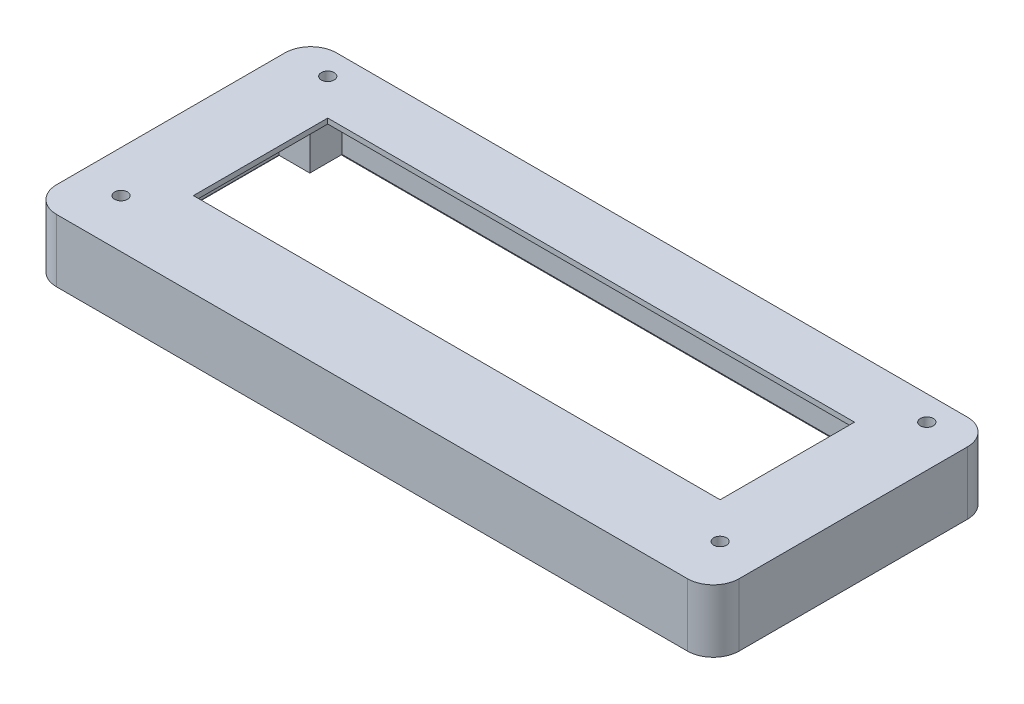
SolidWorks part; units mm, degrees
ref_plane "Front Plane" through (0, 0, 0) normal (0, 0, 1) x (1, 0, 0)
ref_plane "Top Plane" through (0, 0, 0) normal (0, 1, 0) x (1, 0, 0)
ref_plane "Right Plane" through (0, 0, 0) normal (1, 0, 0) x (0, 0, -1)
ref_plane "Plane1" through (0, 80.1151, 0) normal (0, 1, 0) x (1, 0, 0)
sketch "Sketch1" plane through (0, 80.1151, 0) normal (0, 1, 0) x (1, 0, 0)
  line L8 (100.7602, -83.1642) -> (100.7602, -109.1842)
  line L9 (-1.2398, -109.1842) -> (100.7602, -109.1842)
  line L10 (-1.2398, -83.1642) -> (-1.2398, -109.1842)
  line L11 (-1.2398, -83.1642) -> (100.7602, -83.1642)
  line L16 (115.8352, -125.5842) -> (115.8352, -71.3842)
  line L17 (-16.3148, -125.5842) -> (115.8352, -125.5842)
  line L18 (-16.3148, -71.3842) -> (-16.3148, -125.5842)
  line L19 (115.8352, -71.3842) -> (-16.3148, -71.3842)
  line L20 (115.8352, -125.5842) -> (115.8352, -71.3842)
  line L21 (-16.3148, -125.5842) -> (115.8352, -125.5842)
  line L22 (-16.3148, -71.3842) -> (-16.3148, -125.5842)
  line L23 (115.8352, -71.3842) -> (-16.3148, -71.3842)
  line L25 (-2.7398, -81.6642) -> (102.2602, -81.6642) construction
  line L26 (-2.7398, -81.6642) -> (-2.7398, -110.6842) construction
  line L27 (-2.7398, -110.6842) -> (102.2602, -110.6842) construction
  line L28 (102.2602, -81.6642) -> (102.2602, -110.6842) construction
  dimension "D1" = 5
  dimension "D2" = 1.5
extrude "Boss-Extrude6" add sketch "Sketch1" against normal offset from surface (12.15 mm away) 0.5
ref_plane "Plane2" through (0, 79.1151, 0) normal (0, 1, 0) x (1, 0, 0)
sketch "Sketch3" plane through (0, 79.1151, 0) normal (0, 1, 0) x (1, 0, 0)
  line L0 (110.8352, -120.5842) -> (110.8352, -76.3842) construction
  line L5 (-2.7398, -81.6642) -> (102.2602, -81.6642)
  line L6 (-2.7398, -81.6642) -> (-2.7398, -110.6842)
  line L7 (-2.7398, -110.6842) -> (102.2602, -110.6842)
  line L8 (102.2602, -81.6642) -> (102.2602, -110.6842)
  line L9 (-11.3148, -76.3842) -> (110.8352, -76.3842)
  line L10 (-11.3148, -76.3842) -> (-11.3148, -120.5842)
  line L11 (-11.3148, -120.5842) -> (110.8352, -120.5842)
  line L12 (110.8352, -76.3842) -> (110.8352, -120.5842)
  line L13 (-11.3148, -120.5842) -> (110.8352, -120.5842) construction
extrude "Cut-Extrude9" cut sketch "Sketch3" against normal up to body separate body contours L12 L9 L10 L11 L5 L8 L7 L6
sketch "Sketch4" plane through (0, 67.9651, 0) normal (0, -1, 0) x (1, 0, 0)
  line L8 (111.3352, 121.0842) -> (-11.8148, 121.0842)
  line L9 (111.3352, 75.8842) -> (111.3352, 121.0842)
  line L10 (-11.8148, 75.8842) -> (111.3352, 75.8842)
  line L11 (-11.8148, 121.0842) -> (-11.8148, 75.8842)
  line L12 (111.3352, 121.0842) -> (-11.8148, 121.0842)
  line L13 (111.3352, 75.8842) -> (111.3352, 121.0842)
  line L14 (-11.8148, 75.8842) -> (111.3352, 75.8842)
  line L15 (-11.8148, 121.0842) -> (-11.8148, 75.8842)
  dimension "D1" = 0.5
extrude "Cut-Extrude10" cut sketch "Sketch4" against normal up to surface separate body
sketch "Sketch5" plane through (0, 70.1151, 0) normal (0, -1, 0) x (1, 0, 0)
  point P0 (-7.8148, 117.0842)
  point P1 (107.3352, 117.0842)
  point P3 (107.3352, 79.8842)
  point P5 (-7.8148, 79.8842)
hole_wizard "Tap Drill for M3x0.5 Tap1" positions "Sketch6" profile "Sketch7" hole size "M3x0.5" standard "ANSI Metric"
sketch "Sketch6" plane through (0, 70.1151, 0) normal (0, -1, 0) x (-1, 0, 0)
  point P0 (-107.3352, -79.8842)
  point P3 (-107.3352, -117.0842)
  point P6 (7.8148, -117.0842)
  point P9 (7.8148, -79.8842)
sketch "Sketch7" plane through (107.3352, 70.1151, 79.8842) normal (1, 0, 0) x (0, 0, -1)
  line L0 (0, 0) -> (0, 4.7511)
  line L1 (0, 4.7511) -> (1.25, 4)
  line L2 (1.25, 4) -> (1.25, 0)
  line L5 (1.25, 0) -> (0, 0)
  line L10 (0, 4.7511) -> (-1.25, 4) construction
  line L11 (0, -6.35) -> (0, 107.95) construction
  dimension "Hole Dia." = 2.5
  dimension "Hole Depth" = 4
  dimension "Drill Angle" = 118
sketch "Sketch8" plane through (0, 70.1151, 0) normal (0, -1, 0) x (1, 0, 0)
  line L16 (103.2602, 77.8842) -> (103.2602, 114.8842)
  line L17 (-3.7398, 77.8842) -> (103.2602, 77.8842)
  line L18 (-3.7398, 84.1342) -> (-3.7398, 77.8842)
  line L19 (-9.7398, 84.1342) -> (-3.7398, 84.1342)
  line L20 (-9.7398, 109.1342) -> (-9.7398, 84.1342)
  line L21 (-3.7398, 109.1342) -> (-9.7398, 109.1342)
  line L22 (-3.7398, 114.8842) -> (-3.7398, 109.1342)
  line L23 (103.2602, 114.8842) -> (-3.7398, 114.8842)
  line L24 (103.2602, 77.8842) -> (103.2602, 114.8842)
  line L25 (-3.7398, 77.8842) -> (103.2602, 77.8842)
  line L26 (-3.7398, 84.1342) -> (-3.7398, 77.8842)
  line L27 (-9.7398, 84.1342) -> (-3.7398, 84.1342)
  line L28 (-9.7398, 109.1342) -> (-9.7398, 84.1342)
  line L29 (-3.7398, 109.1342) -> (-9.7398, 109.1342)
  line L30 (-3.7398, 114.8842) -> (-3.7398, 109.1342)
  line L31 (103.2602, 114.8842) -> (-3.7398, 114.8842)
  dimension "D1" = 0.5
extrude "Cut-Extrude11" cut sketch "Sketch8" against normal up to surface (9 mm away)
fillet "Fillet1" radius 5 4 edges at (-16.3148, 74.0401, 125.5842) (115.8352, 74.0401, 125.5842) (115.8352, 74.0401, 71.3842) (-16.3148, 74.0401, 71.3842)
sketch "Sketch9" plane through (0, 80.1151, 0) normal (0, 1, 0) x (1, 0, 0)
  line L0 (50.4294, -76.1642) -> (50.4294, -83.1642) construction
  line L1 (-8.2398, -76.1642) -> (107.7602, -76.1642) construction
  line L2 (-8.2398, -76.1642) -> (-8.2398, -116.1842) construction
  line L3 (-8.2398, -116.1842) -> (107.7602, -116.1842) construction
  line L4 (107.7602, -76.1642) -> (107.7602, -116.1842) construction
  line L5 (100.7602, -83.1642) -> (-1.2398, -83.1642) construction
  line L6 (51.1822, -116.1842) -> (51.1822, -109.1842) construction
  line L7 (-1.2398, -109.1842) -> (100.7602, -109.1842) construction
  line L8 (-1.2398, -83.1642) -> (-8.2398, -76.1642) construction
  line L9 (107.7602, -76.1642) -> (100.7602, -83.1642) construction
  line L10 (107.7602, -116.1842) -> (100.7602, -109.1842) construction
  line L11 (-1.2398, -109.1842) -> (-8.2398, -116.1842) construction
  point P21 (-6.8651, -77.2392)
  point P23 (-9.2907, -78.5774)
  point P24 (107.2385, -76.6859)
  dimension "D1" = 45
  dimension "D2" = 7
hole_wizard "Tap Drill for M3x0.5 Tap2" positions "Sketch10" profile "Sketch11" hole size "M3x0.5" standard "ANSI Metric"
sketch "Sketch10" plane through (0, 80.1151, 0) normal (0, 1, 0) x (1, 0, 0)
  point P0 (-8.2398, -76.1642)
  point P3 (-8.2398, -116.1842)
  point P6 (107.7602, -116.1842)
  point P9 (107.7602, -76.1642)
sketch "Sketch11" plane through (-8.2398, 80.1151, 76.1642) normal (1, 0, 0) x (0, 0, 1)
  line L0 (0, 0) -> (0, 5.7511)
  line L1 (0, 5.7511) -> (1.25, 5)
  line L2 (1.25, 5) -> (1.25, 0)
  line L5 (1.25, 0) -> (0, 0)
  line L10 (0, 5.7511) -> (-1.25, 5) construction
  line L11 (0, -6.35) -> (0, 107.95) construction
  dimension "Hole Dia." = 2.5
  dimension "Hole Depth" = 5
  dimension "Drill Angle" = 118
